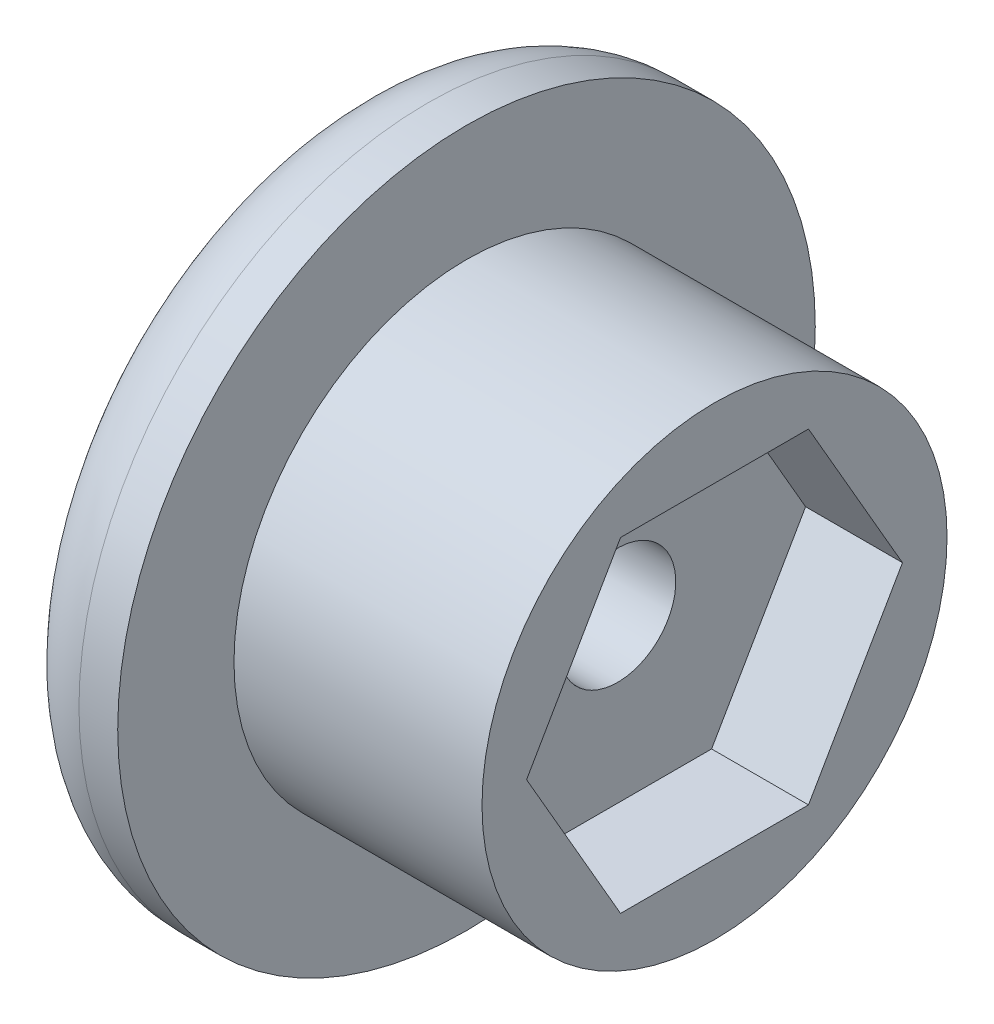
SolidWorks part; units mm, degrees
ref_plane "Alzado" through (0, 0, 0) normal (0, 0, 1) x (1, 0, 0)
ref_plane "Planta" through (0, 0, 0) normal (0, 1, 0) x (1, 0, 0)
ref_plane "Vista lateral" through (0, 0, 0) normal (1, 0, 0) x (0, 0, -1)
sketch "Croquis1" plane through (-24.6696, 0, 0) normal (-1, 0, 0) x (0, 0, 1)
  line L0 (67.5594, -4.9363) -> (62.9406, -4.9363) construction
  line L1 (67.6749, -4.7363) -> (62.8251, -4.7363)
  line L2 (62.8251, -4.7363) -> (60.4003, -8.9363)
  line L3 (60.4003, -8.9363) -> (62.8251, -13.1363)
  line L4 (62.8251, -13.1363) -> (67.6749, -13.1363)
  line L5 (67.6749, -13.1363) -> (70.0997, -8.9363)
  line L6 (70.0997, -8.9363) -> (67.6749, -4.7363)
  circle A0 centre (65.25, -8.9363) radius 4.2 construction
  circle A1 centre (65.25, -8.9363) radius 6
  dimension "D2" = 12
  dimension "D1" = 0.2
extrude "Saliente-Extruir1" add sketch "Croquis1" along normal blind 2.5
sketch "Croquis2" plane through (-27.1696, 0, 0) normal (-1, 0, 0) x (0, 0, 1)
  circle A0 centre (65.25, -8.9363) radius 6 construction
  circle A1 centre (65.25, -8.9363) radius 6
extrude "Saliente-Extruir2" add sketch "Croquis2" along normal blind 5.5
sketch "Croquis3" plane through (-32.6696, 0, 0) normal (-1, 0, 0) x (0, 0, 1)
  circle A0 centre (65.25, -8.9363) radius 1.5
  dimension "D1" = 3
extrude "Cortar-Extruir1" cut sketch "Croquis3" against normal blind 12.5
sketch "Croquis4" plane through (-32.6696, 0, 0) normal (-1, 0, 0) x (0, 0, 1)
  circle A0 centre (65.25, -8.9363) radius 3
  dimension "D1" = 6
extrude "Cortar-Extruir2" cut sketch "Croquis4" against normal blind 3
ref_plane "Plano1" through (-31.0696, 0, 0) normal (-1, 0, 0) x (0, 0, 1)
sketch "Croquis5" plane through (-31.0696, 0, 0) normal (-1, 0, 0) x (0, 0, 1)
  circle A0 centre (65.25, -8.9363) radius 3
  circle A1 centre (65.25, -8.9363) radius 9
  dimension "D1" = 18
extrude "Saliente-Extruir3" add sketch "Croquis5" along normal blind 3
fillet "Redondeo1" radius 2 1 edges at (-34.0696, -17.9363, 65.25)
